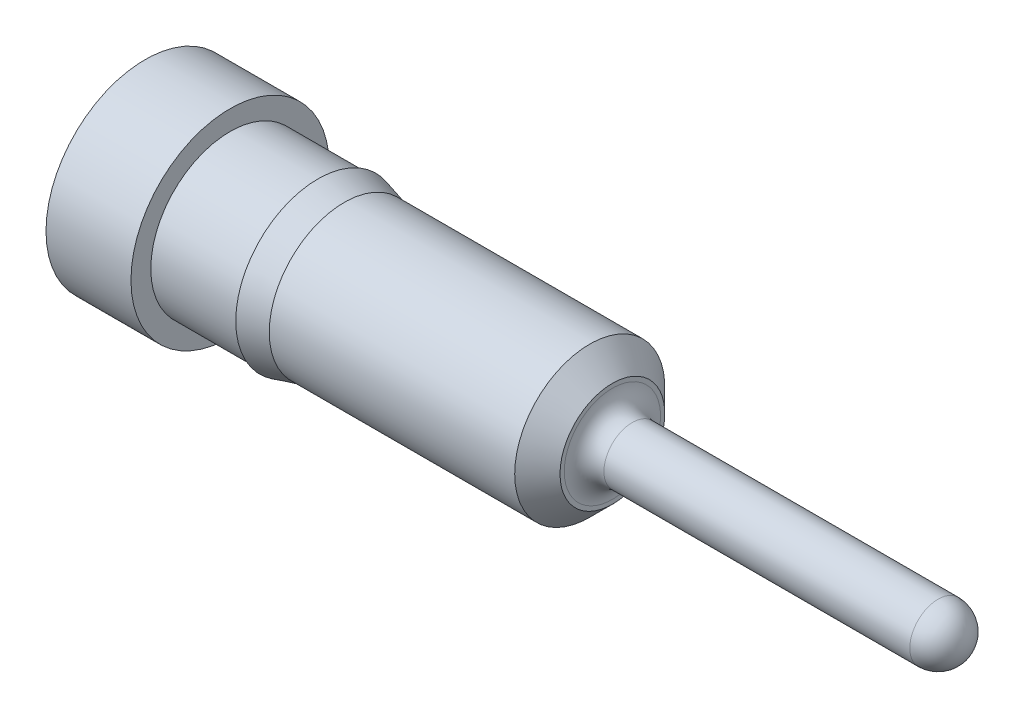
SolidWorks part; units mm, degrees
material "Brass Alloy 385"
ref_plane "Front Plane" through (0, 0, 0) normal (0, 0, 1) x (1, 0, 0)
ref_plane "Top Plane" through (0, 0, 0) normal (0, 1, 0) x (1, 0, 0)
ref_plane "Right Plane" through (0, 0, 0) normal (1, 0, 0) x (0, 0, -1)
sketch "Sketch1" plane through (0, 0, 0) normal (0, 0, 1) x (1, 0, 0)
  line L0 (4.191, 0.4699) -> (4.191, 0.4318)
  line L1 (3.9878, 0.6731) -> (4.191, 0.4699)
  line L2 (1.7864, 0.6731) -> (3.9878, 0.6731)
  line L3 (1.5494, 0.7366) -> (1.7864, 0.6731)
  line L4 (1.5494, 0.7112) -> (1.5494, 0.7366)
  line L5 (0.762, 0.7112) -> (1.5494, 0.7112)
  line L6 (0.762, 0.889) -> (0.762, 0.7112)
  line L7 (0, 0.889) -> (0.762, 0.889)
  line L8 (0, 0) -> (0, 0.889)
  line L9 (0, 0) -> (7.366, 0)
  line L10 (4.3688, 0.254) -> (7.112, 0.254)
  line L11 (0, 0) -> (7.366, 0) construction
  arc A0 (7.366, 0) -> (7.112, 0.254) centre (7.112, 0) ccw
  arc A1 (4.191, 0.4318) -> (4.3688, 0.254) centre (4.3688, 0.4318) ccw
revolve "RevolutionAngle1" add sketch "Sketch1" angle 360 about L11
